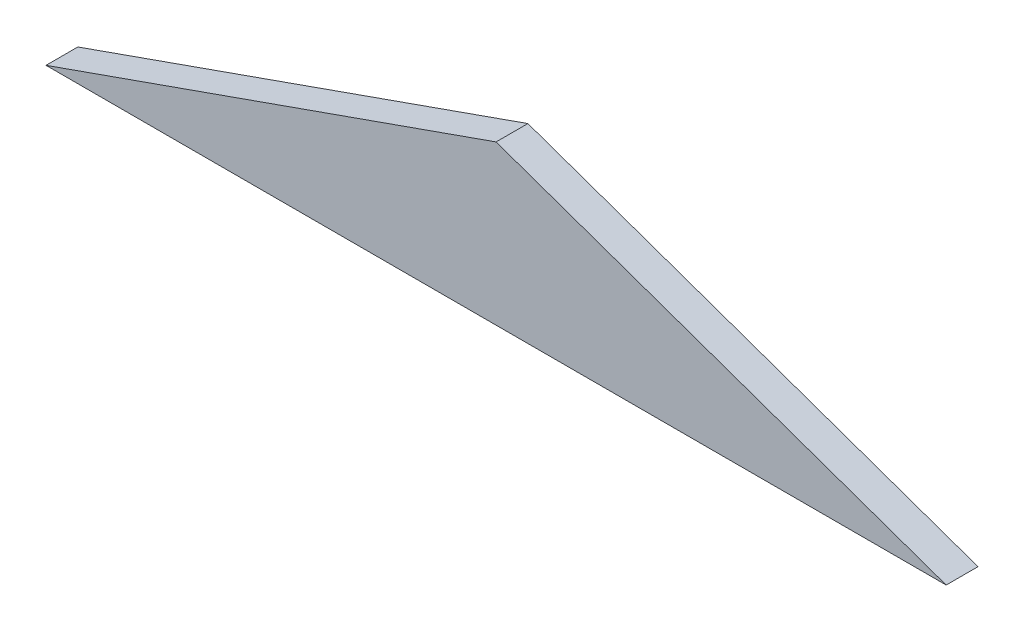
SolidWorks part; units mm, degrees
ref_plane "Plan de face" through (0, 0, 0) normal (0, 0, 1) x (1, 0, 0)
ref_plane "Plan de dessus" through (0, 0, 0) normal (0, 1, 0) x (1, 0, 0)
ref_plane "Plan de droite" through (0, 0, 0) normal (1, 0, 0) x (0, 0, -1)
sketch "Esquisse1" plane through (0, 0, 0) normal (0, 0, 1) x (1, 0, 0)
  line L0 (42.4386, 95.0346) -> (-42.4386, 95.0346)
  line L1 (-42.4386, 95.0346) -> (0, 110)
  line L2 (0, 110) -> (0, 95.0346) construction
  line L3 (-1.5625, 109.449) -> (-162.8292, 52.5805) construction
  line L4 (42.4386, 95.0346) -> (0, 110)
  dimension "D1" = 45
extrude "Boss.-Extru.1" add sketch "Esquisse1" along normal blind 3
